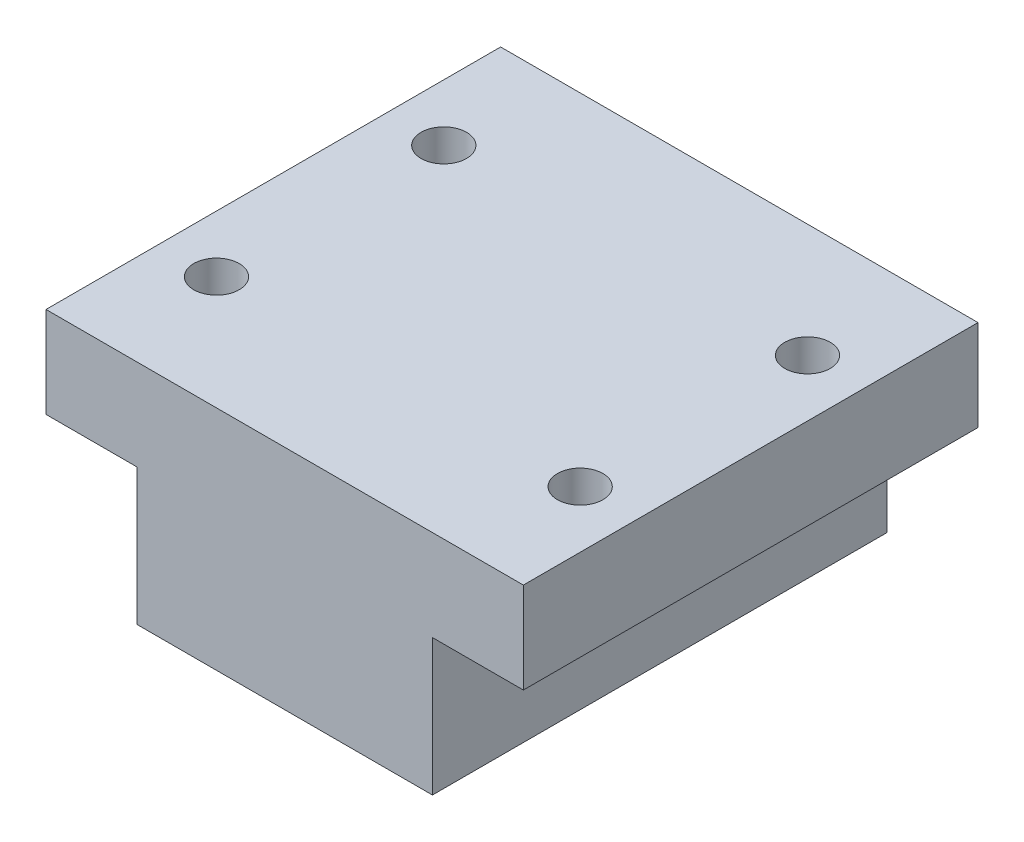
SolidWorks part; units mm, degrees
ref_plane "Front Plane" through (0, 0, 0) normal (0, 0, 1) x (1, 0, 0)
ref_plane "Top Plane" through (0, 0, 0) normal (0, 1, 0) x (1, 0, 0)
ref_plane "Right Plane" through (0, 0, 0) normal (1, 0, 0) x (0, 0, -1)
sketch "Sketch1" plane through (0, 0, 0) normal (0, 0, 1) x (1, 0, 0)
  line L0 (13, -4) -> (21, -4)
  line L1 (-21, -4) -> (-13, -4)
  line L2 (-21, -4) -> (-21, 4)
  line L3 (-21, 4) -> (21, 4)
  line L4 (21, -4) -> (21, 4)
  line L5 (-21, -4) -> (21, 4) construction
  line L6 (-21, 4) -> (21, -4) construction
  line L8 (13, -4) -> (13, -16)
  line L9 (13, -16) -> (-13, -16)
  line L10 (-13, -4) -> (-13, -16)
  point P0 (0, 0)
  dimension "D1" = 42
  dimension "D2" = 8
  dimension "D3" = 12
  dimension "D4" = 26
  dimension "D5" = 8
extrude "Boss-Extrude1" add sketch "Sketch1" along normal mid plane 40
sketch "Sketch2" plane through (0, 4, 0) normal (0, 1, 0) x (1, 0, 0)
  line L0 (-16, -10) -> (16, -10) construction
  line L1 (16, -10) -> (16, 10) construction
  line L2 (16, 10) -> (-16, 10) construction
  line L3 (-16, 10) -> (-16, -10) construction
  line L5 (-21, 20) -> (-13, 20) construction
  line L6 (-13, -20) -> (-13, 20) construction
  circle A0 centre (-16, 10) radius 2
  circle A1 centre (16, 10) radius 2
  circle A2 centre (-16, -10) radius 2
  circle A3 centre (16, -10) radius 2
  dimension "D1" = 4
  dimension "D2" = 4
  dimension "D3" = 4
  dimension "D4" = 4
  dimension "D5" = 32
  dimension "D6" = 20
  dimension "D7" = 10
  dimension "D8" = 3
extrude "Cut-Extrude1" cut sketch "Sketch2" against normal blind 40
sketch "Sketch4" plane through (0, -16, 0) normal (0, -1, 0) x (1, 0, 0)
  line L0 (-13, -20) -> (13, -20) construction
  line L2 (0, 0) -> (0, -4.5) construction
  circle A0 centre (0, -4.5) radius 5.5
  dimension "D1" = 15.5
  dimension "D2" = 11
extrude "Cut-Extrude2" cut sketch "Sketch4" against normal blind 1.75
